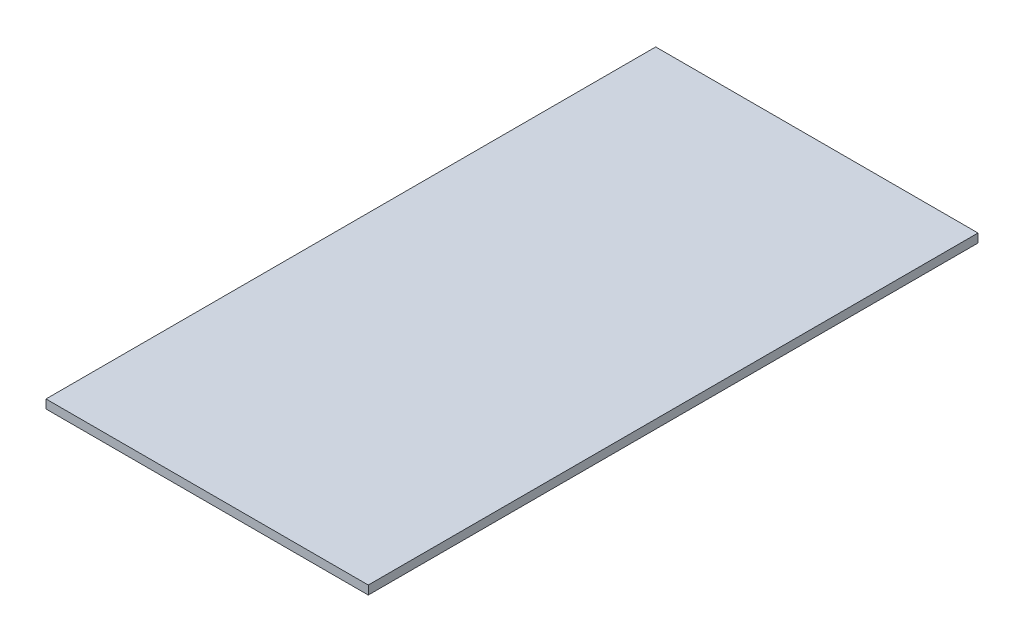
SolidWorks part; units mm, degrees
ref_plane "Front Plane" through (0, 0, 0) normal (0, 0, 1) x (1, 0, 0)
ref_plane "Top Plane" through (0, 0, 0) normal (0, 1, 0) x (1, 0, 0)
ref_plane "Right Plane" through (0, 0, 0) normal (1, 0, 0) x (0, 0, -1)
sketch "Sketch1" plane through (0, 0, 0) normal (0, 1, 0) x (1, 0, 0)
  line L1 (-469.9, -889) -> (469.9, -889)
  line L2 (-469.9, -889) -> (-469.9, 889)
  line L3 (-469.9, 889) -> (469.9, 889)
  line L4 (469.9, -889) -> (469.9, 889)
  line L5 (-469.9, -889) -> (469.9, 889) construction
  line L6 (-469.9, 889) -> (469.9, -889) construction
  point P0 (0, 0)
  dimension "D1" = 939.8
  dimension "D2" = 1778
extrude "Boss-Extrude1" add sketch "Sketch1" along normal blind 25.4
